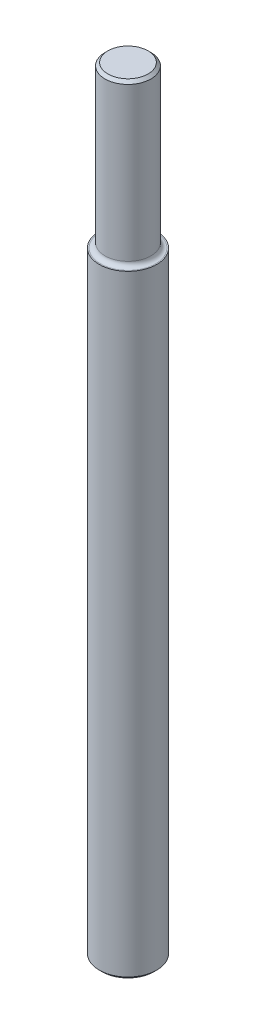
SolidWorks part; units mm, degrees
material " 40Х ГОСТ 4543-71"
ref_plane "Спереди" through (0, 0, 0) normal (0, 0, 1) x (1, 0, 0)
ref_plane "Сверху" through (0, 0, 0) normal (0, 1, 0) x (1, 0, 0)
ref_plane "Слева" through (0, 0, 0) normal (1, 0, 0) x (0, 0, -1)
sketch "Эскиз1" plane through (0, 0, 0) normal (0, 1, 0) x (1, 0, 0)
  circle A0 centre (0, 0) radius 10
  dimension "D1" = 20
extrude "Вытянуть1" add sketch "Эскиз1" along normal blind 270
sketch "Эскиз2" plane through (0, 270, 0) normal (0, 1, 0) x (1, 0, 0)
  circle A0 centre (0, 0) radius 8
  dimension "D1" = 16
extrude "Вытянуть2" cut sketch "Эскиз2" against normal blind 56 flip side to cut
cosmetic thread "Условное изображение резьбы1" parameters "D1"=54, "D2"=15.9999
fillet "Скругление1" radius 1.6 1 edges at (0, 214, 8)
chamfer "Фаска1" distance 1 angle 45 2 edges at (0, 0, 10) (0, 270, 8)
